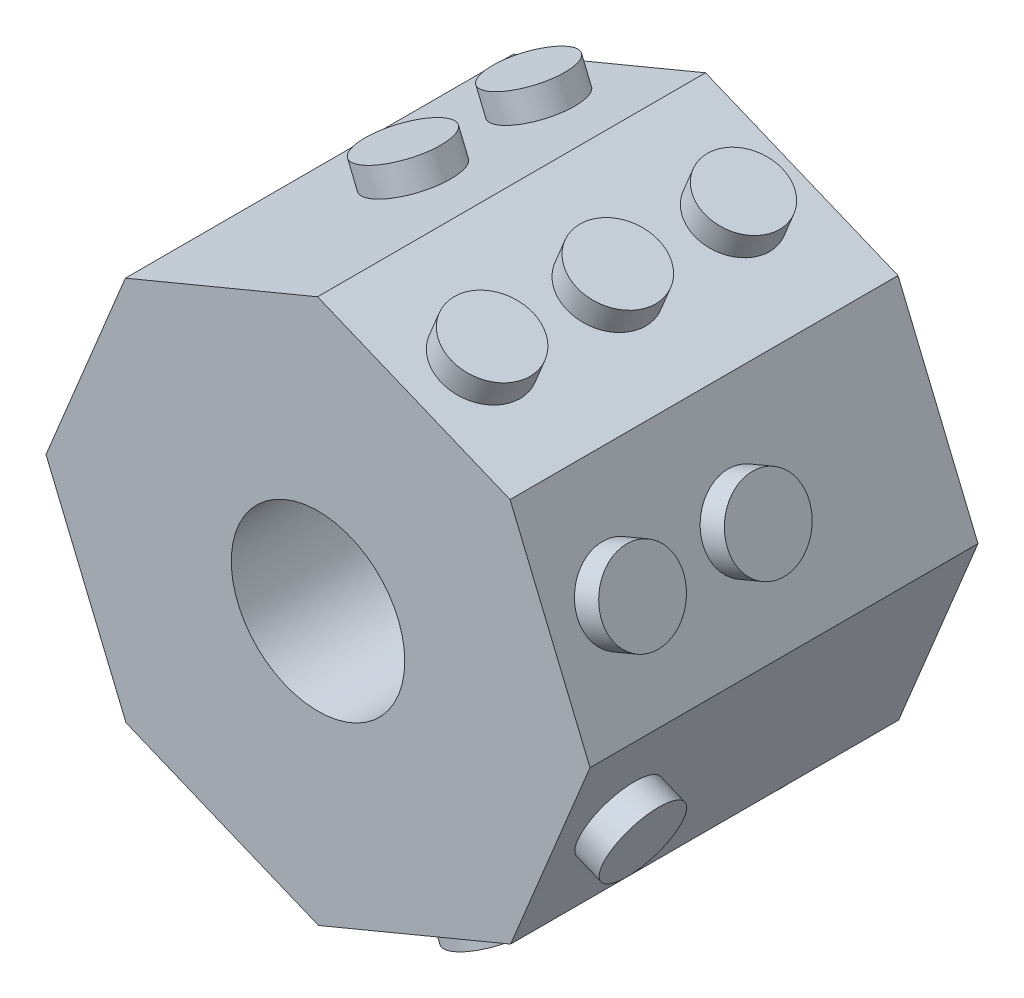
SolidWorks part; units mm, degrees
ref_plane "Front Plane" through (0, 0, 0) normal (0, 0, 1) x (1, 0, 0)
ref_plane "Top Plane" through (0, 0, 0) normal (0, 1, 0) x (1, 0, 0)
ref_plane "Right Plane" through (0, 0, 0) normal (1, 0, 0) x (0, 0, -1)
sketch "Sketch1" plane through (0, 0, 0) normal (0, 0, 1) x (1, 0, 0)
  line L1 (-0.0078, 4.978) -> (-3.5255, 3.5145)
  line L2 (-3.5255, 3.5145) -> (-4.978, -0.0078)
  line L3 (-4.978, -0.0078) -> (-3.5145, -3.5255)
  line L4 (-3.5145, -3.5255) -> (0.0078, -4.978)
  line L5 (0.0078, -4.978) -> (3.5255, -3.5145)
  line L6 (3.5255, -3.5145) -> (4.978, 0.0078)
  line L7 (4.978, 0.0078) -> (3.5145, 3.5255)
  line L8 (3.5145, 3.5255) -> (-0.0078, 4.978)
  circle A0 centre (0, 0) radius 4.5991 construction
  dimension "D1" = 3.81
extrude "Boss-Extrude1" add sketch "Sketch1" along normal blind 7.1
sketch "Sketch2" plane through (1.7533, 4.2517, 0) normal (0.3812, 0.9245, 0) x (0.9245, -0.3812, 0)
  line L0 (1.905, -7.1) -> (-1.905, -7.1) construction
  circle A0 centre (0, -1.25) radius 0.7146
  circle A1 centre (0, -3.55) radius 0.75
  circle A2 centre (0, -5.85) radius 0.75
  point P9 (0, -7.1)
  dimension "D1" = 1.4292
  dimension "D3" = 1.5
  dimension "D5" = 1.5
  dimension "D2" = 1.25
  dimension "D4" = 2.3
  dimension "D6" = 2.3
  dimension "D7" = 1.25
extrude "Boss-Extrude2" add sketch "Sketch2" along normal blind 0.48
sketch "Sketch8" plane through (4.2462, 1.7666, 0) normal (0.9233, 0.3841, 0) x (0, 0, -1)
  line L1 (-7.1, -1.905) -> (-7.1, 1.905) construction
  circle A1 centre (-3.55, 0) radius 0.75
  circle A2 centre (-5.85, 0) radius 0.75
  dimension "D3" = 2.3
  dimension "D4" = 1.25
extrude "Boss-Extrude4" add sketch "Sketch8" along normal blind 0.48
sketch "Sketch9" plane through (4.2517, -1.7533, 0) normal (0.9245, -0.3812, 0) x (0, 0, -1)
  line L0 (-7.1, -1.905) -> (-7.1, 1.905) construction
  circle A1 centre (-5.85, 0) radius 0.75
  dimension "D1" = 1.25
extrude "Boss-Extrude5" add sketch "Sketch9" along normal blind 0.48
sketch "Sketch10" plane through (1.7666, -4.2462, 0) normal (0.3841, -0.9233, 0) x (0.9233, 0.3841, 0)
  line L0 (-1.905, 7.1) -> (1.905, 7.1) construction
  circle A0 centre (0, 5.85) radius 0.7146
  circle A2 centre (0, 1.25) radius 0.75
  dimension "D1" = 1.25
  dimension "D2" = 1.25
extrude "Boss-Extrude7" add sketch "Sketch10" along normal blind 0.48
sketch "Sketch11" plane through (-1.7666, 4.2462, 0) normal (-0.3841, 0.9233, 0) x (0.9233, 0.3841, 0)
  line L0 (1.905, 0) -> (-1.905, 0) construction
  circle A0 centre (-0.048, -1.25) radius 0.7146
  circle A1 centre (-0.048, -3.55) radius 0.75
  dimension "D1" = 1.25
  dimension "D2" = 2.3
extrude "Boss-Extrude8" add sketch "Sketch11" along normal blind 0.48
sketch "Sketch12" plane through (-4.2517, 1.7533, 0) normal (-0.9245, 0.3812, 0) x (0, 0, 1)
  circle A0 centre (1.25, 0) radius 0.7146
  dimension "D1" = 1.25
extrude "Boss-Extrude9" add sketch "Sketch12" along normal blind 0.48
sketch "Sketch13" plane through (-1.7533, -4.2517, 0) normal (-0.3812, -0.9245, 0) x (0.9245, -0.3812, 0)
  circle A1 centre (0, 3.55) radius 0.75
extrude "Boss-Extrude10" add sketch "Sketch13" along normal blind 0.48
sketch "Sketch15" plane through (0, 0, 7.1) normal (0, 0, 1) x (1, 0, 0)
  circle A0 centre (0, 0) radius 1.5875
  dimension "D1" = 3.175
extrude "Cut-Extrude3" cut sketch "Sketch15" against normal through all
